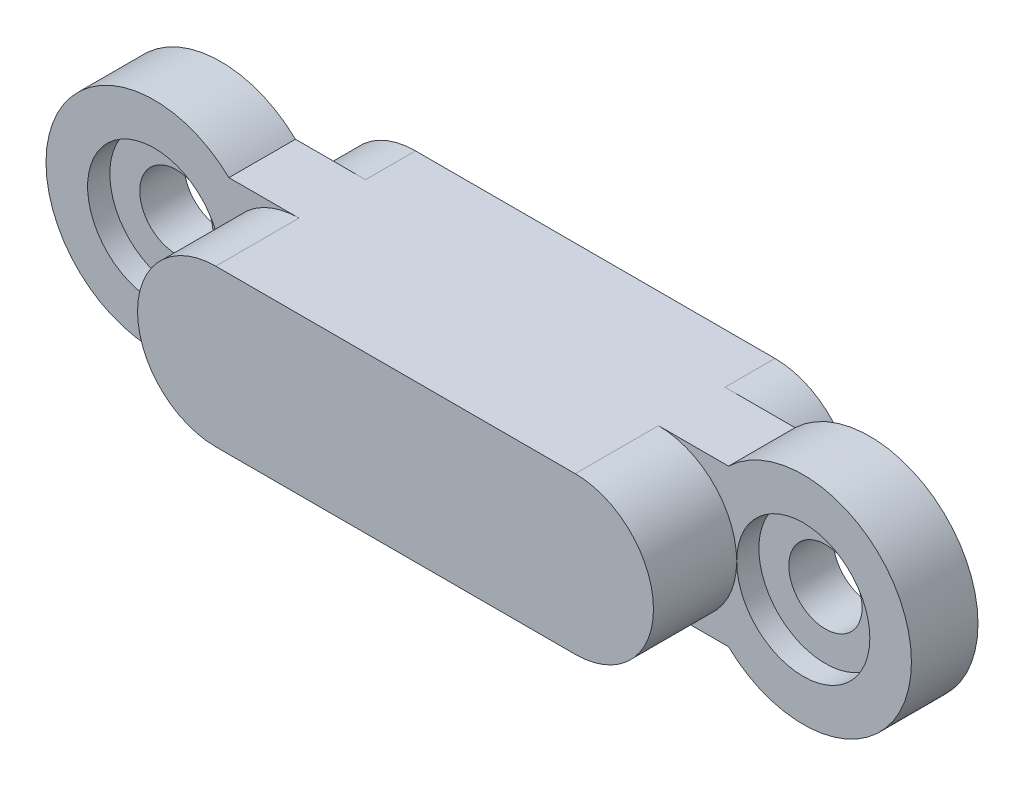
SolidWorks part; units mm, degrees
ref_plane "Спереди" through (0, 0, 0) normal (0, 0, 1) x (1, 0, 0)
ref_plane "Сверху" through (0, 0, 0) normal (0, 1, 0) x (1, 0, 0)
ref_plane "Справа" through (0, 0, 0) normal (1, 0, 0) x (0, 0, -1)
sketch "Эскиз4" plane through (0, 0, 1.9) normal (0, 0, 1) x (1, 0, 0)
  line L1 (0, -4.7) -> (10.8, -4.7)
  line L2 (0, -4.7) -> (0, 0)
  line L3 (0, 0) -> (10.8, 0)
  line L4 (10.8, -4.7) -> (10.8, 0)
  circle A0 centre (0, -2.35) radius 2.35
  circle A1 centre (10.8, -2.35) radius 2.35
  point P0 (6.7714, -2.35)
  dimension "D1" = 4.7
  dimension "D2" = 10.8
extrude "Бобышка-Вытянуть4" add sketch "Эскиз4" along normal blind 2.5 separate body
sketch "Эскиз5" plane through (0, 0, 1.9) normal (0, 0, -1) x (-1, 0, 0)
  line L6 (-15.15, 0) -> (4.35, 0)
  line L7 (-15.15, 0) -> (-15.15, -4.7)
  line L8 (-15.15, -4.7) -> (4.35, -4.7)
  line L9 (4.35, 0) -> (4.35, -4.7)
  circle A0 centre (-15.15, -2.35) radius 1.1
  circle A1 centre (4.35, -2.35) radius 1.1
  circle A2 centre (-15.15, -2.35) radius 3.25
  circle A3 centre (4.35, -2.35) radius 3.25
  arc M13 (0, -4.7) -> (0, 0) centre (0, -2.35) ccw
  line M14 (0, 0) -> (-10.8, 0)
  arc M15 (-10.8, 0) -> (-10.8, -4.7) centre (-10.8, -2.35) ccw
  line M16 (-10.8, -4.7) -> (0, -4.7)
  dimension "D1" = 19.5
extrude "Бобышка-Вытянуть5" add sketch "Эскиз5" along normal blind 2 contours L6 A2 L8 L7 A0 | A2 L6 L7 A0 L8 M15 | A2 L6 M15 | A3 A2 M13 M14 M15 M16 | A2 M15 | A2 L8 M15 | A3 M13 | A3 L6 M13 | A3 L8 M13 | L6 A3 L8 L9 A1 M13 | L8 A3 L6 L9 A1
sketch "Эскиз6" plane through (0, 0, 1.9) normal (0, 0, 1) x (1, 0, 0)
  circle A0 centre (15.15, -2.35) radius 2
  circle A1 centre (-4.35, -2.35) radius 2
extrude "Вырез-Вытянуть1" cut sketch "Эскиз6" against normal blind 0.6667
sketch "Эскиз7" plane through (0, 0, -0.1) normal (0, 0, -1) x (-1, 0, 0)
  line L0 (-5.4, 0) -> (0, 0)
  line L6 (-10.8, -4.7) -> (0, -4.7)
  line L7 (-10.8, -4.7) -> (-10.8, 0)
  line L8 (-10.8, 0) -> (0, 0)
  line L9 (0, -4.7) -> (0, 0)
  circle A0 centre (-10.8, -2.35) radius 2.35
  circle A1 centre (0, -2.35) radius 2.35
  point P0 (-5.4, -2.35)
  point P1 (-5.4, -2.35)
extrude "Бобышка-Вытянуть6" add sketch "Эскиз7" along normal blind 1.5 contours L8 L7 L6 L9 | A0 | A1
sketch "Эскиз8" plane through (0, 0, -1.6) normal (0, 0, -1) x (-1, 0, 0)
  circle A0 centre (-5.4, -2.35) radius 0.5
  dimension "D1" = 1
extrude "Бобышка-Вытянуть7" add sketch "Эскиз8" along normal blind 1.5
